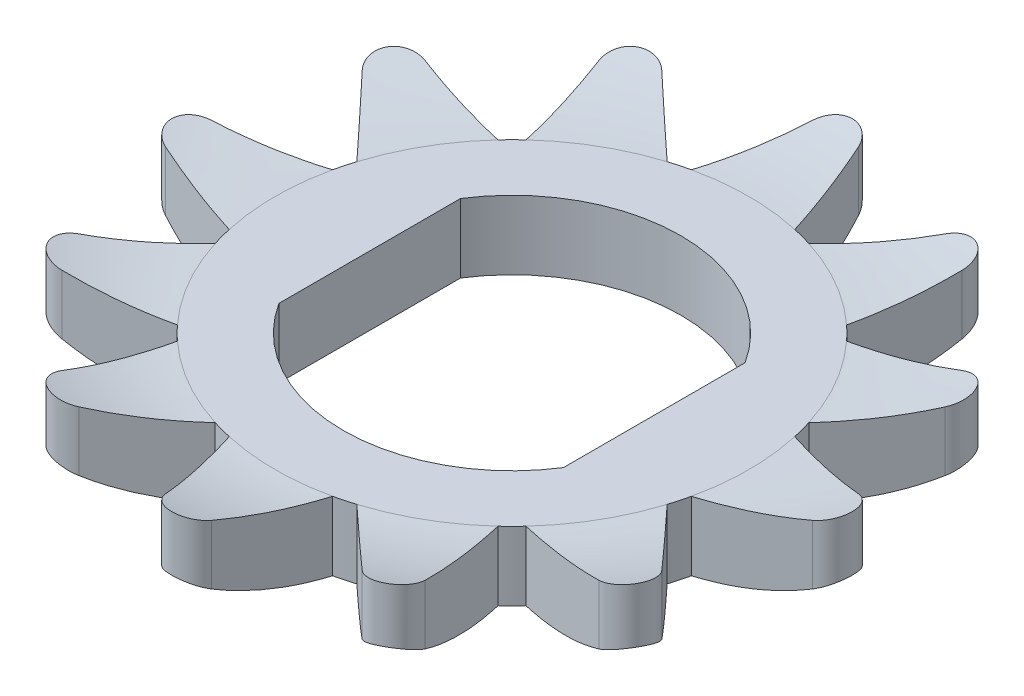
SolidWorks part; units mm, degrees
material "1060 Alloy"
ref_plane "Front Plane" through (0, 0, 0) normal (0, 0, 1) x (1, 0, 0)
ref_plane "Top Plane" through (0, 0, 0) normal (0, 1, 0) x (1, 0, 0)
ref_plane "Right Plane" through (0, 0, 0) normal (1, 0, 0) x (0, 0, -1)
sketch "Sketch1" plane through (0, 0, 0) normal (0, 1, 0) x (1, 0, 0)
  line L0 (0, 6.875) -> (0, 9.88) construction
  line L1 (-1.5, 6.7094) -> (-0.6685, 9.3876)
  line L2 (0.6685, 9.3876) -> (1.5, 6.7094)
  line L3 (2.0556, 6.5605) -> (4.1148, 8.4641)
  line L4 (5.2727, 7.7956) -> (4.6537, 5.0605)
  line L5 (5.0605, 4.6537) -> (7.7956, 5.2727)
  line L6 (8.4641, 4.1148) -> (6.5605, 2.0556)
  line L7 (6.7094, 1.5) -> (9.3876, 0.6685)
  line L8 (9.3876, -0.6685) -> (6.7094, -1.5)
  line L9 (6.5605, -2.0556) -> (8.4641, -4.1148)
  line L10 (7.7956, -5.2727) -> (5.0605, -4.6537)
  line L11 (4.6537, -5.0605) -> (5.2727, -7.7956)
  line L12 (4.1148, -8.4641) -> (2.0556, -6.5605)
  line L13 (1.5, -6.7094) -> (0.6685, -9.3876)
  line L14 (-0.6685, -9.3876) -> (-1.5, -6.7094)
  line L15 (-2.0556, -6.5605) -> (-4.1148, -8.4641)
  line L16 (-5.2727, -7.7956) -> (-4.6537, -5.0605)
  line L17 (-5.0605, -4.6537) -> (-7.7956, -5.2727)
  line L18 (-8.4641, -4.1148) -> (-6.5605, -2.0556)
  line L19 (-6.7094, -1.5) -> (-9.3876, -0.6685)
  line L20 (-9.3876, 0.6685) -> (-6.7094, 1.5)
  line L21 (-6.5605, 2.0556) -> (-8.4641, 4.1148)
  line L22 (-7.7956, 5.2727) -> (-5.0605, 4.6537)
  line L23 (-4.6537, 5.0605) -> (-5.2727, 7.7956)
  line L24 (-4.1148, 8.4641) -> (-2.0556, 6.5605)
  arc A1 (-4.6537, 5.0605) -> (-5.0605, 4.6537) centre (0, 0) ccw
  arc A2 (-0.6685, 9.3876) -> (0.6685, 9.3876) centre (0, 9.18) cw
  arc A3 (4.1148, 8.4641) -> (5.2727, 7.7956) centre (4.59, 7.9501) cw
  arc A4 (7.7956, 5.2727) -> (8.4641, 4.1148) centre (7.9501, 4.59) cw
  arc A5 (9.3876, 0.6685) -> (9.3876, -0.6685) centre (9.18, 0) cw
  arc A6 (8.4641, -4.1148) -> (7.7956, -5.2727) centre (7.9501, -4.59) cw
  arc A7 (5.2727, -7.7956) -> (4.1148, -8.4641) centre (4.59, -7.9501) cw
  arc A8 (0.6685, -9.3876) -> (-0.6685, -9.3876) centre (0, -9.18) cw
  arc A9 (-4.1148, -8.4641) -> (-5.2727, -7.7956) centre (-4.59, -7.9501) cw
  arc A10 (-7.7956, -5.2727) -> (-8.4641, -4.1148) centre (-7.9501, -4.59) cw
  arc A11 (-9.3876, -0.6685) -> (-9.3876, 0.6685) centre (-9.18, 0) cw
  arc A12 (-8.4641, 4.1148) -> (-7.7956, 5.2727) centre (-7.9501, 4.59) cw
  arc A13 (-5.2727, 7.7956) -> (-4.1148, 8.4641) centre (-4.59, 7.9501) cw
  arc A14 (-6.5605, 2.0556) -> (-6.7094, 1.5) centre (0, 0) ccw
  arc A15 (-6.7094, -1.5) -> (-6.5605, -2.0556) centre (0, 0) ccw
  arc A16 (-5.0605, -4.6537) -> (-4.6537, -5.0605) centre (0, 0) ccw
  arc A17 (-2.0556, -6.5605) -> (-1.5, -6.7094) centre (0, 0) ccw
  arc A18 (1.5, -6.7094) -> (2.0556, -6.5605) centre (0, 0) ccw
  arc A19 (4.6537, -5.0605) -> (5.0605, -4.6537) centre (0, 0) ccw
  arc A20 (6.5605, -2.0556) -> (6.7094, -1.5) centre (0, 0) ccw
  arc A21 (6.7094, 1.5) -> (6.5605, 2.0556) centre (0, 0) ccw
  arc A22 (5.0605, 4.6537) -> (4.6537, 5.0605) centre (0, 0) ccw
  arc A23 (2.0556, 6.5605) -> (1.5, 6.7094) centre (0, 0) ccw
  arc A24 (-1.5, 6.7094) -> (-2.0556, 6.5605) centre (0, 0) ccw
  point P10 (0, 9.88)
  point P69 (0, 0)
  dimension "D1" = 3.005
  dimension "D2" = 13.75
  dimension "D3" = 0.7
  dimension "D4" = 3
  dimension "D5" = 12
extrude "Boss-Extrude1" add sketch "Sketch1" along normal blind 2.45
sketch "Sketch2" plane through (0, 0, 0) normal (1, 0, 0) x (0, 0, -1)
  line L0 (6.875, 0) -> (-6.875, 0)
  line L1 (-7.7956, 0) -> (-5.0605, 0) construction
  line L2 (-1.5, 0) -> (-0.6685, 0) construction
  line L3 (-9.88, 2.45) -> (-9.88, 0.85)
  line L4 (-9.88, 2.45) -> (-9.88, 0) construction
  line L5 (0, 0) -> (0, 2) construction
  line L6 (0, 2) -> (-6.875, 2)
  line L7 (-6.875, 0) -> (-9.88, 0)
  line L8 (-9.88, 0) -> (-9.88, 0.85)
  line L9 (-9.88, 2.45) -> (0, 2.45)
  line L10 (0.6685, 2.45) -> (-0.6685, 2.45) construction
  line L11 (0, 2.45) -> (0, 2)
  arc A0 (-6.875, 0) -> (-9.88, 0.85) centre (-6.875, 5.7368) cw
  arc A1 (-6.875, 2) -> (-9.88, 2.45) centre (-6.875, 12.2584) cw
  dimension "D4" = 10.2584
  dimension "D5" = 5.7368
  dimension "D1" = 13.75
  dimension "D2" = 1.6
  dimension "D3" = 2
revolve "Cut-Revolve1" cut sketch "Sketch2" angle 360 about L5
sketch "Sketch3" plane through (0, 2, 0) normal (0, 1, 0) x (1, 0, 0)
  line L1 (-4.13, -2.6369) -> (-4.13, 2.6369)
  line L2 (4.13, -2.6369) -> (4.13, 2.6369)
  arc A0 (4.13, 2.6369) -> (-4.13, 2.6369) centre (0, 0) ccw
  arc A1 (-4.13, -2.6369) -> (4.13, -2.6369) centre (0, 0) ccw
  point P6 (0, 0)
  dimension "D1" = 9.8
  dimension "D2" = 8.26
extrude "Cut-Extrude1" cut sketch "Sketch3" against normal blind 2.45
